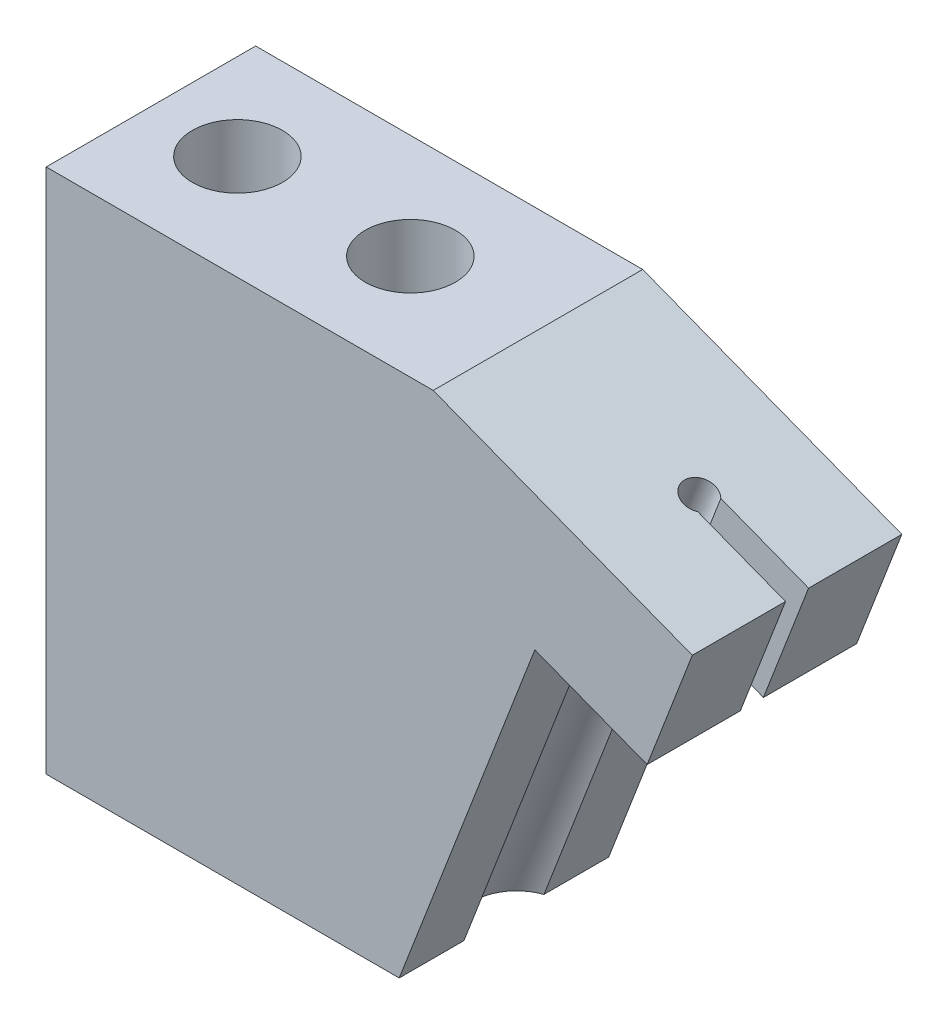
SolidWorks part; units mm, degrees
ref_plane "Front" through (0, 0, 0) normal (0, 0, 1) x (1, 0, 0)
ref_plane "Top" through (0, 0, 0) normal (0, 1, 0) x (1, 0, 0)
ref_plane "Right" through (0, 0, 0) normal (1, 0, 0) x (0, 0, -1)
sketch "Sketch1" plane through (0, 0, 0) normal (0, 0, 1) x (1, 0, 0)
  line L0 (-7.7031, 2.9677) -> (0, 0)
  line L1 (0, 0) -> (7.7031, -2.9677)
  line L2 (-1.9436, 4.731) -> (6.4636, 4.731) construction
  line L3 (0, 0) -> (0, -15.6645) construction
  line L4 (7.7031, -2.9677) -> (1.0375, -20.269)
  line L5 (0, 0) -> (-5.9062, -15.3301) construction
  line L6 (-25.4601, -0.269) -> (-25.4601, -20.269)
  line L7 (-25.4601, -0.269) -> (-8.9501, -0.269)
  line L10 (-25.4601, -20.269) -> (1.0375, -20.269)
  line L11 (-7.7031, 2.9677) -> (-8.9501, -0.269)
  point P7 (1.8227, 4.731)
  dimension "D1" = 21.07
  dimension "D2" = 16.51
  dimension "D3" = 16.51
  dimension "D4" = 25
  dimension "D5" = 20
  dimension "D6" = 5.07
extrude "Base-Extrude" add sketch "Sketch1" along normal mid plane 10
sketch "Sketch2" plane through (0, 0, 5) normal (0, 0, 1) x (1, 0, 0)
  line L0 (-7.7031, 2.9677) -> (7.7031, -2.9677)
  line L1 (7.7031, -2.9677) -> (1.0375, -20.269)
  line L2 (1.0375, -20.269) -> (7.7031, -2.9677) construction
  line L3 (-2.1332, -3.4647) -> (-9.1411, -0.7648)
  line L4 (-7.7031, 2.9677) -> (-9.1411, -0.7648)
  line L5 (-8.6073, -20.269) -> (-2.1332, -3.4647)
  line L7 (-8.6073, -20.269) -> (1.0375, -20.269)
  line L8 (-25.4601, -20.269) -> (1.0375, -20.269) construction
  dimension "D1" = 4
  dimension "D2" = 9
extrude "Cutaway for Clamp Plate & Wire" cut sketch "Sketch2" against normal through all
sketch "Sketch3" plane through (0, 0, 0) normal (0, 0, 1) x (1, 0, 0)
  line L0 (0, 0) -> (-2.873, -7.4572) construction
  line L1 (7.7031, -2.9677) -> (-7.7031, 2.9677) construction
  circle A0 centre (2.4135, -5.2164) radius 2.413
  circle A1 centre (-5.2896, -2.2487) radius 2.413
  dimension "D1" = 4.826
  dimension "D4" = 4.1275
  dimension "D2" = 90
  dimension "D3" = 4
extrude "Clamp Plate Holes (altered to #10-24 OCT04)" cut sketch "Sketch3" against normal up to surface (5 mm away)
sketch "Sketch4" plane through (0, -0.269, 0) normal (0, 1, 0) x (-1, 0, 0)
  line L0 (17.2051, -5) -> (17.2051, 5) construction
  line L1 (8.9501, -5) -> (25.4601, -5) construction
  line L2 (8.9501, 5) -> (25.4601, 5) construction
  line L3 (25.4601, 0) -> (17.2051, 0) construction
  line L5 (25.4601, 5) -> (25.4601, -5) construction
  circle A0 centre (21.3326, 0) radius 2.1527
  circle A1 centre (13.0776, 0) radius 2.1527
  dimension "D1" = 4.3053
extrude "Holes to Pitch Plate" cut sketch "Sketch4" against normal up to surface (20 mm away)
sketch "Sketch5" plane through (-1.438, -3.7326, 0) normal (0.3595, 0.9331, 0) x (-0.9331, 0.3595, 0)
  line L1 (8.255, 5) -> (0, 5)
  line L2 (8.255, 5) -> (8.255, -5)
  line L3 (8.255, -5) -> (0, -5)
  line L4 (0, 5) -> (-5, 5)
  line L5 (4.8209, 0) -> (-7.2676, 0) construction
  line L6 (0, 5) -> (0, -5) construction
  line L7 (0, -5) -> (-5, -5)
  line L8 (-5, 5) -> (-5, -5)
  circle A0 centre (0, 0) radius 2.05
  arc A1 (0, 5) -> (-5, 0) centre (0, 0) ccw construction
  arc A2 (-5, 0) -> (0, -5) centre (0, 0) ccw construction
  dimension "D1" = 4.1
  dimension "D2" = 10
extrude "Extrude1" add sketch "Sketch5" along normal blind 4
ref_plane "Plane1" through (-1.438, -3.7326, 0) normal (-0.3595, -0.9331, 0) x (0.9331, -0.3595, 0)
sketch "Sketch6" plane through (0, 0, 0) normal (0.3595, 0.9331, 0) x (-0.9331, 0.3595, 0)
  line L0 (0, 5) -> (8.255, 5)
  line L1 (8.255, 5) -> (8.255, -5)
  line L2 (8.255, -5) -> (0, -5)
  line L3 (0, 5) -> (-5, 5)
  line L4 (-5, 5) -> (-5, -5)
  line L5 (-5, -5) -> (0, -5)
  arc A0 (0, -5) -> (-5, 0) centre (0, 0) cw construction
  circle A1 centre (0, 0) radius 0.75
  arc A2 (-5, 0) -> (0, 5) centre (0, 0) cw construction
  dimension "D1" = 1.5
extrude "Extrude2" add sketch "Sketch6" along normal blind 2
sketch "Sketch8" plane through (0, -0.269, 0) normal (0, 1, 0) x (-1, 0, 0)
  line L1 (25.4601, -5) -> (6.9841, -5)
  line L2 (25.4601, -5) -> (25.4601, 5)
  line L3 (25.4601, 5) -> (6.9841, 5)
  line L4 (6.9841, -5) -> (6.9841, 5)
  circle A0 centre (21.3326, 0) radius 2.1527
  circle A1 centre (13.0776, 0) radius 2.1527
  circle A2 centre (21.3326, 0) radius 2.1526 construction
  circle A3 centre (13.0776, 0) radius 2.1527 construction
extrude "Extrude3" add sketch "Sketch8" along normal up to vertex (5.103 mm away)
sketch "Sketch7" plane through (-1.438, -3.7326, 0) normal (-0.3595, -0.9331, 0) x (0.9331, -0.3595, 0)
  circle A0 centre (0, 0) radius 2.05
  circle A1 centre (0, 0) radius 2.05 construction
extrude "Cut-Extrude1" cut sketch "Sketch7" along normal through all
sketch "Sketch11" plane through (0.719, 1.8663, 0) normal (0.3595, 0.9331, 0) x (-0.9331, 0.3595, 0)
  circle A0 centre (0, 0) radius 0.75
  circle A1 centre (0, 0) radius 0.75 construction
extrude "Cut-Extrude2" cut sketch "Sketch11" against normal through all
sketch "Sketch12" plane through (4.6657, -1.7975, 0) normal (0.9331, -0.3595, 0) x (0, 0, -1)
  line L0 (-0.55, 2) -> (-0.55, -4)
  line L1 (-5, 2) -> (5, 2) construction
  line L2 (-5, -4) -> (5, -4) construction
  line L3 (-0.55, -4) -> (0.55, -4)
  line L4 (0.55, -4) -> (0.55, 2)
  line L5 (0.55, 2) -> (-0.55, 2)
  line L6 (0, -1.2707) -> (0, 1.4957) construction
  dimension "D1" = 1.1
extrude "Cut-Extrude3" cut sketch "Sketch12" against normal up to next
hole_wizard "#8-32 Tapped Hole1" positions "Sketch14" profile "Sketch13" tap size "#8-32" standard "Ansi Inch"
sketch "Sketch14" plane through (-0.6952, 0.2678, 0) normal (0.9331, -0.3595, 0) x (0, 0, -1)
  line L0 (0.55, -4) -> (5, -4) construction
  point P0 (-0.041, -7.429)
  dimension "D1" = 3.429
sketch "Sketch13" plane through (-3.366, -6.6645, 0.041) normal (0, 0, 1) x (0.3595, 0.9331, 0)
  line L0 (0, 0) -> (0, 7.8958)
  line L1 (0, 7.8958) -> (1.7272, 6.858)
  line L2 (1.7272, 6.858) -> (1.7272, 0)
  line L5 (1.7272, 0) -> (0, 0)
  line L10 (0, 7.8958) -> (-1.7272, 6.858) construction
  line L11 (0, -6.35) -> (0, 107.95) construction
  dimension "Tap Drill Dia." = 3.4544
  dimension "Tap Drill Depth" = 6.858
  dimension "Drill Angle" = 118
